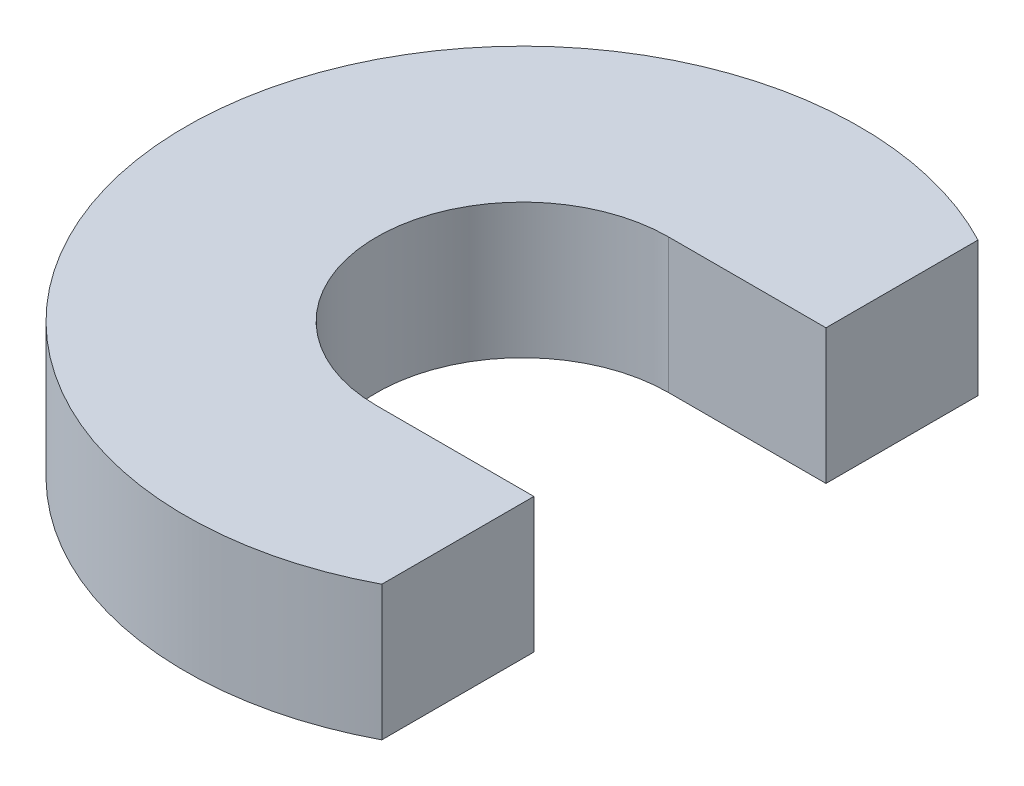
SolidWorks part; units mm, degrees
ref_plane "Front Plane" through (0, 0, 0) normal (0, 0, 1) x (1, 0, 0)
ref_plane "Top Plane" through (0, 0, 0) normal (0, 1, 0) x (1, 0, 0)
ref_plane "Right Plane" through (0, 0, 0) normal (1, 0, 0) x (0, 0, -1)
sketch "Sketch1" plane through (0, 0, 0) normal (0, 1, 0) x (1, 0, 0)
  line L0 (0, 1.651) -> (1.778, 1.651)
  line L1 (0, -1.651) -> (1.778, -1.651)
  line L2 (1.778, -3.3697) -> (1.778, -1.651)
  line L3 (1.778, 1.651) -> (1.778, 3.3697)
  arc A0 (0, 1.651) -> (0, -1.651) centre (0, 0) ccw
  arc A1 (1.778, 3.3697) -> (1.778, -3.3697) centre (0, 0) ccw
  dimension "D1" = 3.302
  dimension "D2" = 7.62
  dimension "D3" = 1.778
extrude "Boss-Extrude1" add sketch "Sketch1" along normal blind 1.524
